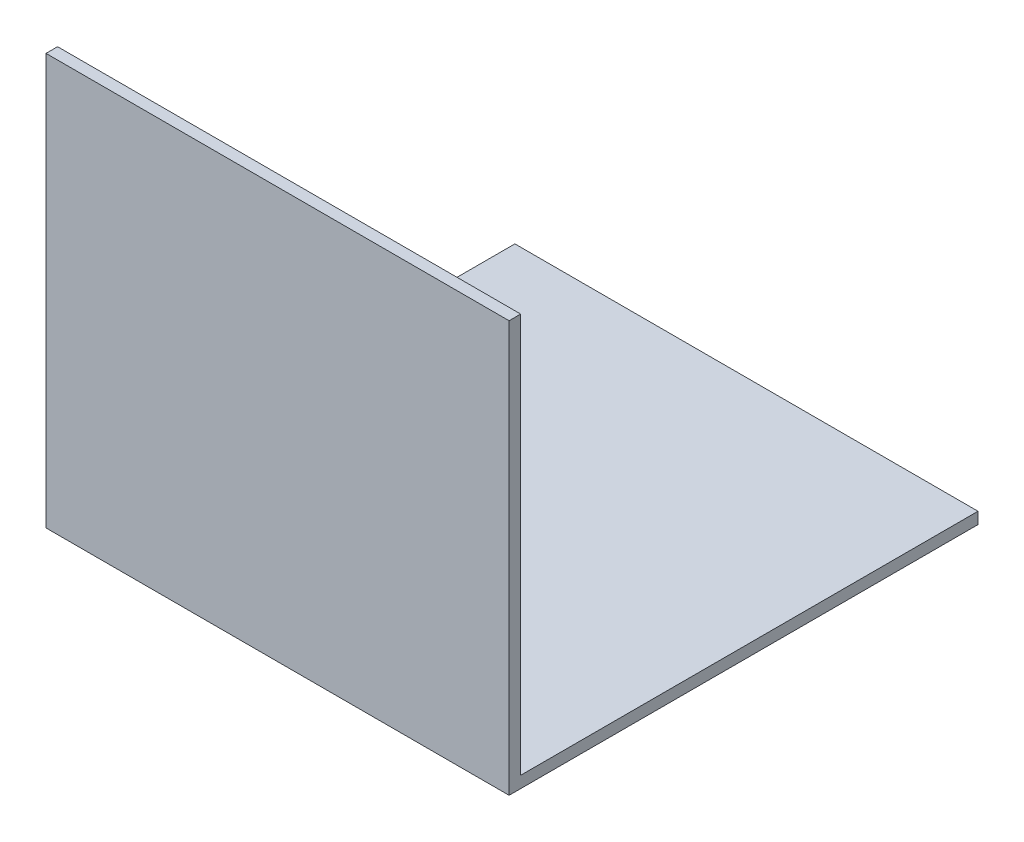
SolidWorks part; units mm, degrees
ref_plane "Front Plane" through (0, 0, 0) normal (0, 0, 1) x (1, 0, 0)
ref_plane "Top Plane" through (0, 0, 0) normal (0, 1, 0) x (1, 0, 0)
ref_plane "Right Plane" through (0, 0, 0) normal (1, 0, 0) x (0, 0, -1)
sketch "Sketch1" plane through (0, 0, 0) normal (1, 0, 0) x (0, 0, -1)
  line L0 (0, 700) -> (0, 0)
  line L1 (0, 0) -> (800, 0)
  dimension "D1" = 700
  dimension "D2" = 800
extrude "Extrude-Thin1" add sketch "Sketch1" along normal blind 800 thin thin type mid plane wall 20
